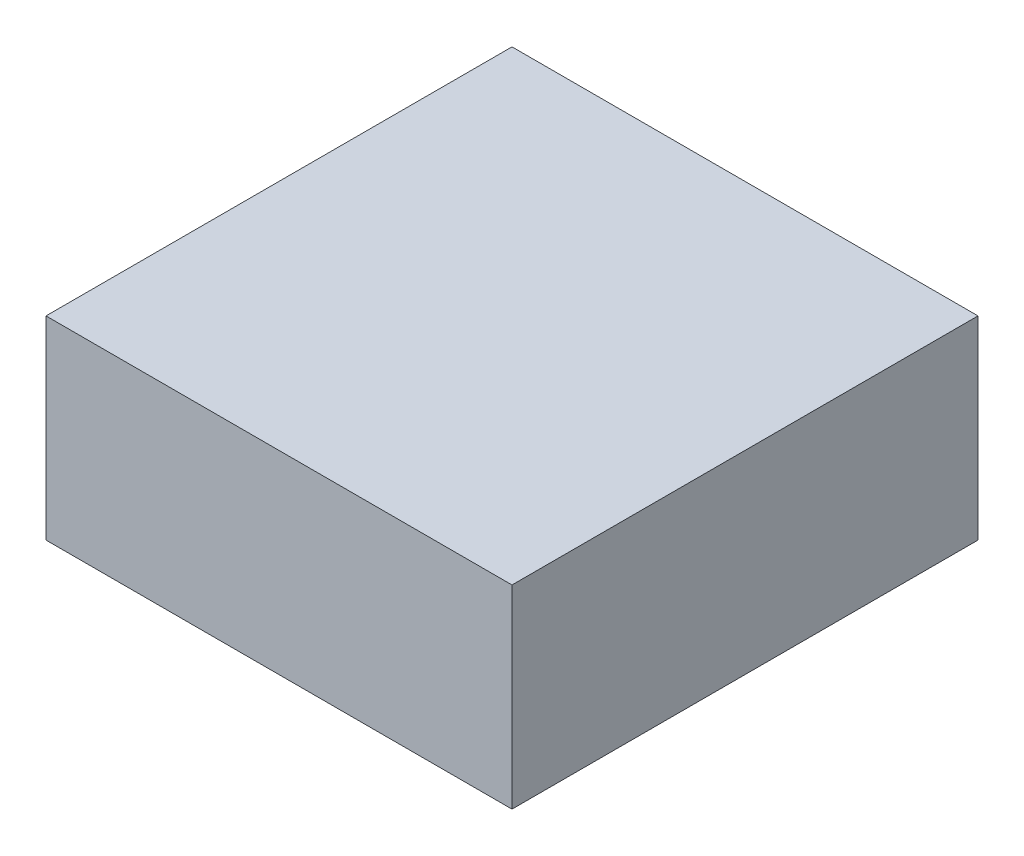
SolidWorks part; units mm, degrees
ref_plane "Front" through (0, 0, 0) normal (0, 0, 1) x (1, 0, 0)
ref_plane "Top" through (0, 0, 0) normal (0, 1, 0) x (1, 0, 0)
ref_plane "Right" through (0, 0, 0) normal (1, 0, 0) x (0, 0, -1)
sketch "草图1" plane through (0, 0, 0) normal (0, 1, 0) x (1, 0, 0)
  line L0 (0, 0) -> (0, 18) construction
  line L1 (0, 18) -> (18, 18) construction
  line L2 (-18, 18) -> (18, 18)
  line L3 (18, 18) -> (18, -18)
  line L4 (0, 0) -> (-18, 0) construction
  line L5 (-18, -18) -> (18, -18)
  line L6 (-18, 18) -> (-18, -18)
  point P7 (18, 0)
  point P9 (0, -18)
extrude "凸台-拉伸1" add sketch "草图1" along normal blind 15
